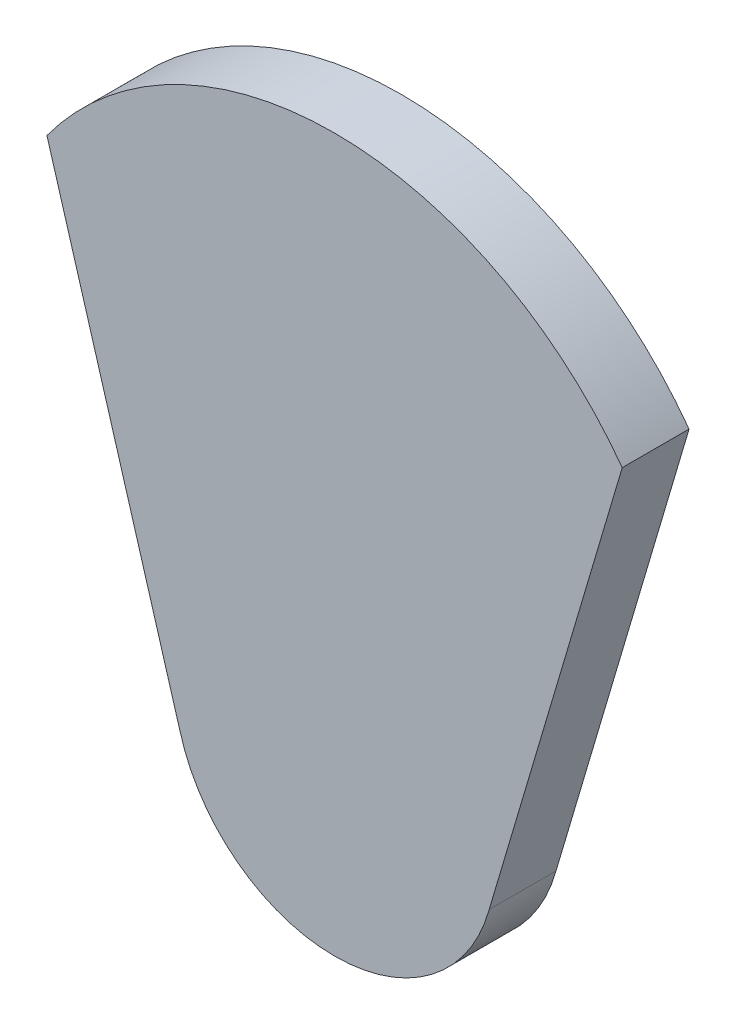
SolidWorks part; units mm, degrees
ref_plane "Front Plane" through (0, 0, 0) normal (0, 0, 1) x (1, 0, 0)
ref_plane "Top Plane" through (0, 0, 0) normal (0, 1, 0) x (1, 0, 0)
ref_plane "Right Plane" through (0, 0, 0) normal (1, 0, 0) x (0, 0, -1)
sketch "Sketch1" plane through (0, 0, 0) normal (0, 0, 1) x (1, 0, 0)
  line L0 (-840.1936, 0) -> (783.1901, 0) construction
  line L1 (0, 0) -> (0, -1117.6) construction
  line L2 (0, 0) -> (0, 1246.1176) construction
  line L3 (-1639.9655, 1199.8071) -> (-881.2738, -1361.4931)
  line L4 (1639.9655, 1199.8071) -> (881.2738, -1361.4931)
  circle A0 centre (0, -1117.6) radius 914.4
  arc A1 (-1639.9655, 1199.8071) -> (1639.9655, 1199.8071) centre (0, 0) cw
  dimension "D1" = 1828.8
  dimension "D3" = 2032
  dimension "D2" = 33
  dimension "D4" = 1117.6
extrude "Boss-Extrude1" add sketch "Sketch1" along normal blind 381 contours A0 | A1 L3 A0 L4
